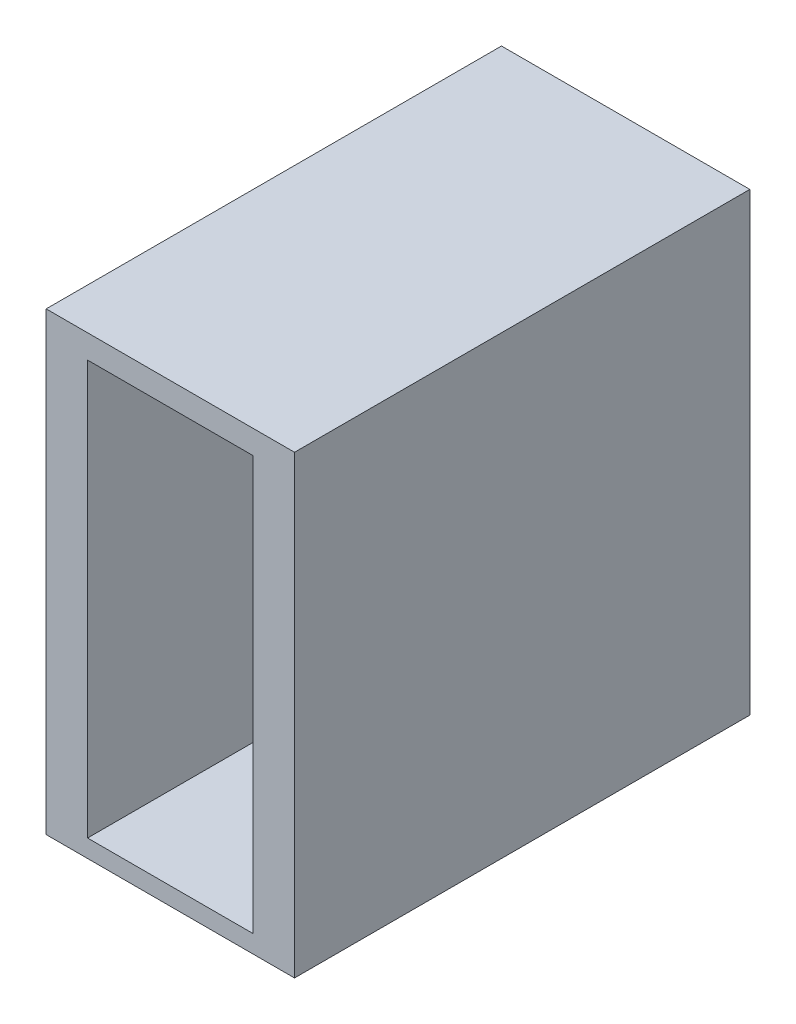
SolidWorks part; units mm, degrees
ref_plane "Front Plane" through (0, 0, 0) normal (0, 0, 1) x (1, 0, 0)
ref_plane "Top Plane" through (0, 0, 0) normal (0, 1, 0) x (1, 0, 0)
ref_plane "Right Plane" through (0, 0, 0) normal (1, 0, 0) x (0, 0, -1)
sketch "Sketch2" plane through (0, 0, 0) normal (0, 1, 0) x (1, 0, 0)
  line L1 (0, 0) -> (12, 0)
  line L2 (0, 0) -> (0, 22)
  line L3 (0, 22) -> (12, 22)
  line L4 (12, 0) -> (12, 22)
  dimension "D1" = 12
  dimension "D2" = 22
extrude "Boss-Extrude1" add sketch "Sketch2" along normal blind 22
sketch "Sketch4" plane through (0, 0, 0) normal (0, 0, 1) x (1, 0, 0)
  line L0 (0, 22) -> (0, 0) construction
  line L1 (2, 20.8577) -> (10, 20.8577)
  line L2 (2, 20.8577) -> (2, 0.8577)
  line L3 (2, 0.8577) -> (10, 0.8577)
  line L4 (10, 20.8577) -> (10, 0.8577)
  dimension "D1" = 8
  dimension "D2" = 20
  dimension "D3" = 2
extrude "Cut-Extrude1" cut sketch "Sketch4" against normal blind 18
sketch "Sketch6" plane through (0, 0, -18) normal (0, 0, 1) x (1, 0, 0)
  line L0 (6, 2.5577) -> (6, 19.1577) construction
  line L1 (5, 2.5577) -> (5, 19.1577)
  line L2 (7, 2.5577) -> (7, 19.1577)
  line L3 (2, 0.8577) -> (10, 0.8577) construction
  line L4 (10, 20.8577) -> (2, 20.8577) construction
  line L5 (10, 0.8577) -> (10, 20.8577) construction
  line L6 (2, 20.8577) -> (2, 0.8577) construction
  arc A0 (5, 2.5577) -> (7, 2.5577) centre (6, 2.5577) ccw
  arc A1 (7, 19.1577) -> (5, 19.1577) centre (6, 19.1577) ccw
  point P2 (6, 10.8577)
  dimension "D2" = 1.7
  dimension "D3" = 1
  dimension "D1" = 2
  dimension "D4" = 1.7
  dimension "D5" = 3
  dimension "D6" = 3
extrude "Cut-Extrude2" cut sketch "Sketch6" against normal blind 10
